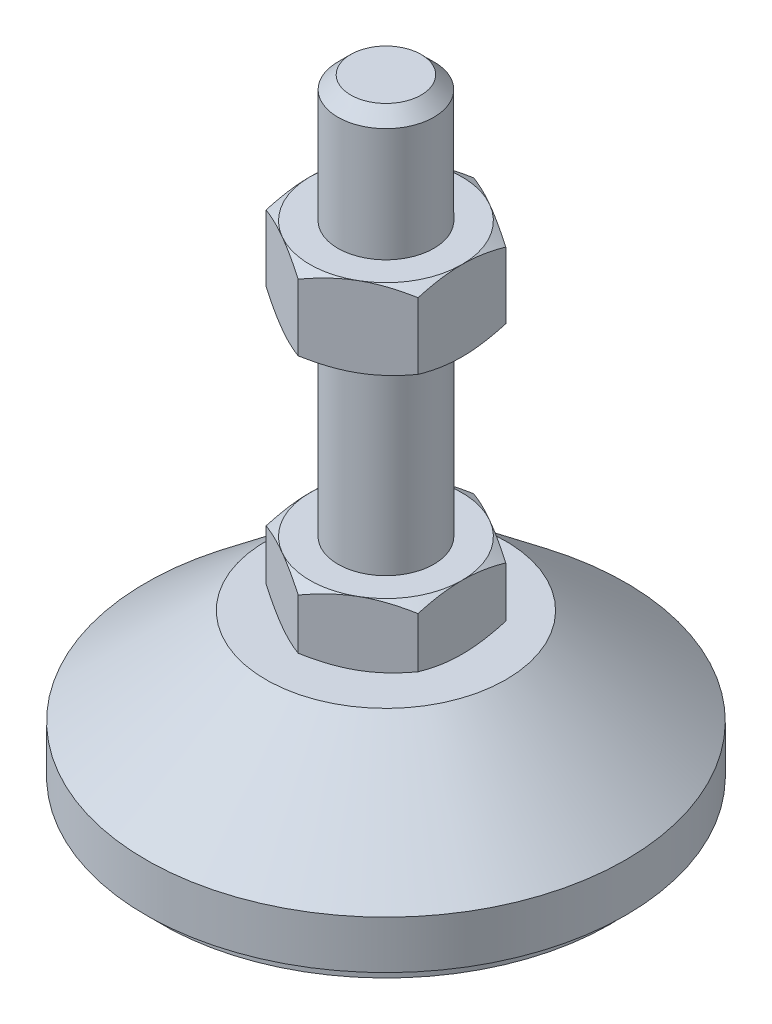
SolidWorks part; units mm, degrees
ref_plane "Спереди" through (0, 0, 0) normal (0, 0, 1) x (1, 0, 0)
ref_plane "Сверху" through (0, 0, 0) normal (0, 1, 0) x (1, 0, 0)
ref_plane "Справа" through (0, 0, 0) normal (1, 0, 0) x (0, 0, -1)
sketch "Эскиз1" plane through (0, 0, 0) normal (0, 0, 1) x (1, 0, 0)
  line L0 (0, 0) -> (-28, 0)
  line L1 (-28, 0) -> (-28, 2)
  line L2 (-28, 2) -> (-30, 2)
  line L3 (-30, 2) -> (-30, 8)
  line L4 (-30, 8) -> (-15, 20)
  line L5 (-15, 20) -> (-6, 20)
  line L12 (-6, 28) -> (-6, 76.4)
  line L13 (-6, 76.4) -> (-4.4, 78)
  line L14 (-4.4, 78) -> (0, 78)
  line L15 (0, 78) -> (0, 0) construction
  line L16 (-6, 20) -> (0, 20) construction
  line L17 (0, 0) -> (0, 78)
  line L18 (0, 0) -> (0, -7.9595) construction
  line L19 (-6, 28) -> (-6, 20)
  point P8 (-6, 52.2)
  point P23 (-10.5, 20)
  dimension "D1" = 12
  dimension "D2" = 20
  dimension "D3" = 8
  dimension "D4" = 60
  dimension "D5" = 6
  dimension "D6" = 1.6
  dimension "D7" = 45
  dimension "D8" = 30
  dimension "D9" = 2
  dimension "D10" = 50
  dimension "D11" = 6
revolve "Повернуть1" add sketch "Эскиз1" angle 360 about L17
sketch "Эскиз2" plane through (0, 20, 0) normal (0, 1, 0) x (1, 0, 0)
  line L1 (0, 10.9697) -> (-9.5, 5.4848)
  line L2 (-9.5, 5.4848) -> (-9.5, -5.4848)
  line L3 (-9.5, -5.4848) -> (0, -10.9697)
  line L4 (0, -10.9697) -> (9.5, -5.4848)
  line L5 (9.5, -5.4848) -> (9.5, 5.4848)
  line L6 (9.5, 5.4848) -> (0, 10.9697)
  circle A0 centre (0, 0) radius 9.5 construction
  dimension "D1" = 19
extrude "Бобышка-Вытянуть1" add sketch "Эскиз2" along normal up to vertex (8 mm away) up to point (-6, 28, 0)
ref_plane "Плоскость1" through (0, 52.2, 0) normal (0, 1, 0) x (1, 0, 0)
sketch "Эскиз3" plane through (0, 52.2, 0) normal (0, 1, 0) x (1, 0, 0)
  line L6 (9.5, 5.4848) -> (0, 10.9697)
  line L7 (0, 10.9697) -> (-9.5, 5.4848)
  line L8 (-9.5, 5.4848) -> (-9.5, -5.4848)
  line L9 (-9.5, -5.4848) -> (0, -10.9697)
  line L10 (0, -10.9697) -> (9.5, -5.4848)
  line L11 (9.5, -5.4848) -> (9.5, 5.4848)
  line L12 (9.5, 5.4848) -> (0, 10.9697)
  line L13 (0, 10.9697) -> (-9.5, 5.4848)
  line L14 (-9.5, 5.4848) -> (-9.5, -5.4848)
  line L15 (-9.5, -5.4848) -> (0, -10.9697)
  line L16 (0, -10.9697) -> (9.5, -5.4848)
  line L17 (9.5, -5.4848) -> (9.5, 5.4848)
  dimension "D1" = 0
extrude "Бобышка-Вытянуть2" add sketch "Эскиз3" along normal blind 10
sketch "Эскиз4" plane through (0, 0, 0) normal (0, 0, 1) x (1, 0, 0)
  line L0 (-9.5, 62.2) -> (-18.1603, 57.2)
  line L1 (-18.1603, 57.2) -> (-18.1603, 62.2)
  line L2 (-18.1603, 62.2) -> (-9.5, 62.2)
  line L3 (-18.1603, 57.2) -> (-9.5, 52.2)
  line L4 (50, 52.2) -> (-50, 52.2) construction
  line L5 (-9.5, 52.2) -> (-18.1603, 52.2)
  line L6 (-18.1603, 52.2) -> (-18.1603, 57.2)
  line L7 (-9.5, 62.2) -> (-9.5, 52.2) construction
  line L8 (-9.5, 28) -> (-16.4282, 28)
  line L9 (-16.4282, 28) -> (-16.4282, 24)
  line L10 (-16.4282, 24) -> (-9.5, 28)
  line L11 (-9.5, 20) -> (-16.4282, 24)
  line L12 (-16.4282, 24) -> (-16.4282, 20)
  line L13 (-16.4282, 20) -> (-9.5, 20)
  line L14 (0, 78) -> (0, 96.3793) construction
  dimension "D1" = 30
  dimension "D2" = 30
revolve "Вырез-Повернуть2" cut sketch "Эскиз4" angle 360 about L14
